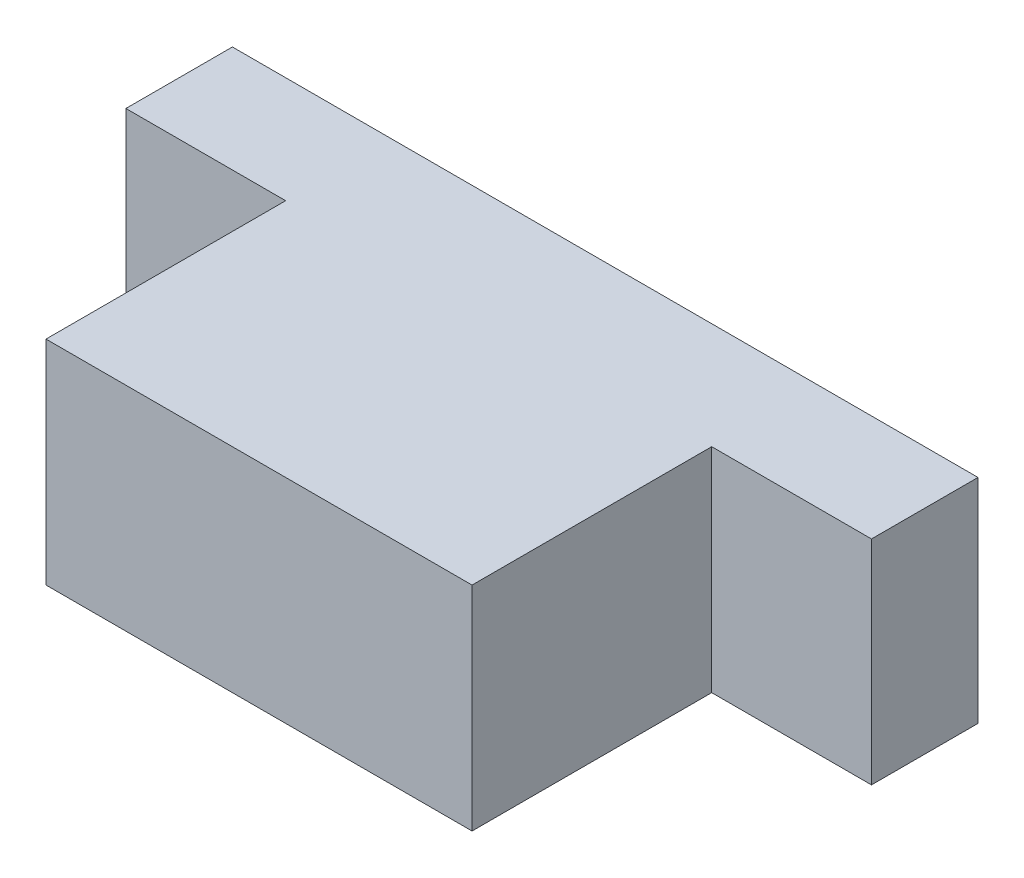
SolidWorks part; units mm, degrees
material "Pine"
ref_plane "Front Plane" through (0, 0, 0) normal (0, 0, 1) x (1, 0, 0)
ref_plane "Top Plane" through (0, 0, 0) normal (0, 1, 0) x (1, 0, 0)
ref_plane "Right Plane" through (0, 0, 0) normal (1, 0, 0) x (0, 0, -1)
sketch "Sketch1" plane through (0, 0, 0) normal (0, 0, 1) x (1, 0, 0)
  line L1 (-20, -10) -> (20, -10)
  line L2 (-20, -10) -> (-20, 10)
  line L3 (-20, 10) -> (20, 10)
  line L4 (20, -10) -> (20, 10)
  line L5 (-20, -10) -> (20, 10) construction
  line L6 (-20, 10) -> (20, -10) construction
  point P0 (0, 0)
  dimension "D1" = 40
  dimension "D2" = 20
extrude "Boss-Extrude1" add sketch "Sketch1" along normal blind 22.5
sketch "Sketch2" plane through (0, 0, 0) normal (0, 0, -1) x (-1, 0, 0)
  line L1 (-35, -10) -> (35, -10)
  line L2 (-35, -10) -> (-35, 10)
  line L3 (-35, 10) -> (35, 10)
  line L4 (35, -10) -> (35, 10)
  line L5 (-35, -10) -> (35, 10) construction
  line L6 (-35, 10) -> (35, -10) construction
  point P0 (0, 0)
  dimension "D1" = 20
  dimension "D2" = 70
extrude "Boss-Extrude2" add sketch "Sketch2" along normal blind 10
